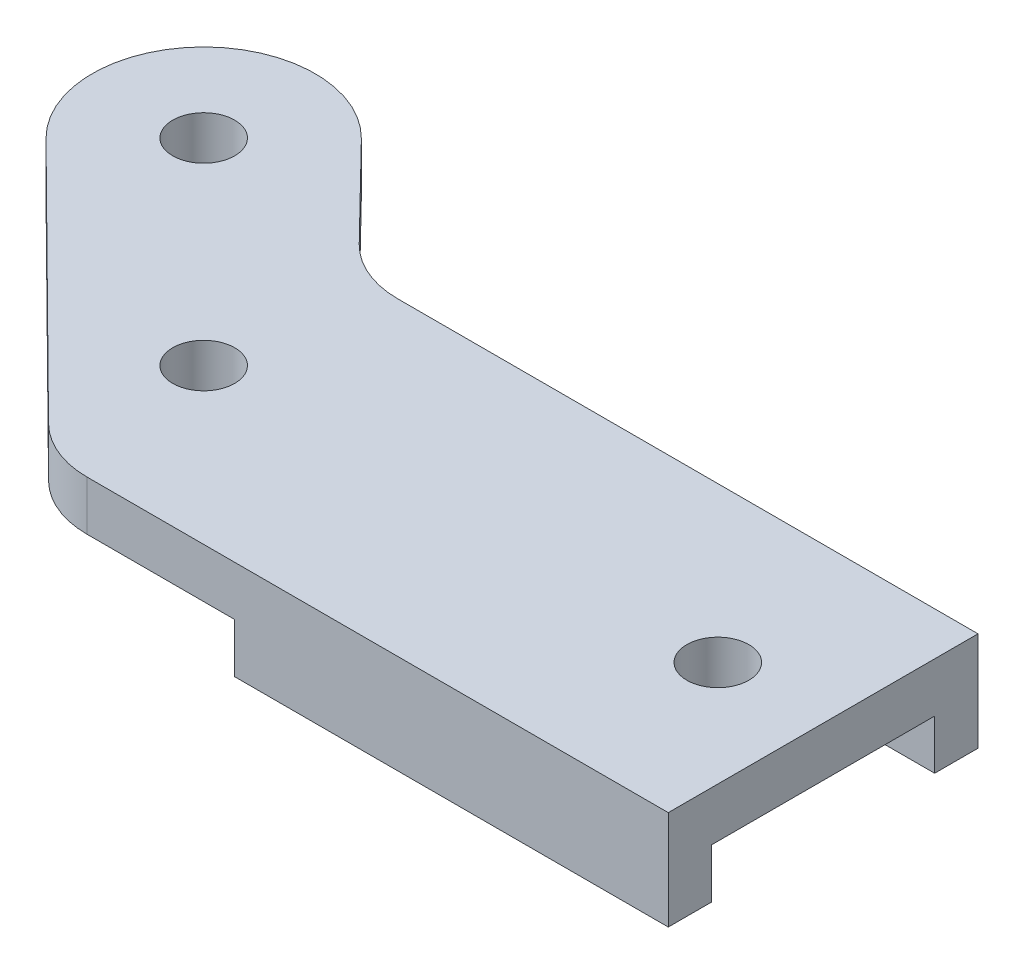
SolidWorks part; units mm, degrees
ref_plane "Front Plane" through (0, 0, 0) normal (0, 0, 1) x (1, 0, 0)
ref_plane "Top Plane" through (0, 0, 0) normal (0, 1, 0) x (1, 0, 0)
ref_plane "Right Plane" through (0, 0, 0) normal (1, 0, 0) x (0, 0, -1)
sketch "Sketch1" plane through (0, 0, 0) normal (0, 1, 0) x (1, 0, 0)
  line L0 (0, 0) -> (100, 0) construction
  line L1 (0, -25) -> (100, -25)
  line L2 (0, 25) -> (100, 25)
  line L3 (0, 0) -> (-31.8198, 31.8198) construction
  line L4 (0, 25) -> (-18.942, 44.3961)
  line L5 (0, -25) -> (-44.4821, 19.0265)
  line L6 (100, 25) -> (100, -25)
  circle A0 centre (-31.8198, 31.8198) radius 5
  circle A1 centre (0, 0) radius 5
  circle A2 centre (83, 0) radius 5
  arc A3 (-18.942, 44.3961) -> (-44.4821, 19.0265) centre (-31.8198, 31.8198) ccw
  dimension "D5" = 36
  dimension "D1" = 100
  dimension "D3" = 45
  dimension "D4" = 135
  dimension "D6" = 17
  dimension "D2" = 25
extrude "Boss-Extrude1" add sketch "Sketch1" along normal blind 8
sketch "Sketch2" plane through (0, 0, 0) normal (0, -1, 0) x (1, 0, 0)
  line L0 (100, 25) -> (30, 25)
  line L1 (0, 25) -> (100, 25) construction
  line L2 (30, 25) -> (30, -25)
  line L3 (100, -25) -> (0, -25) construction
  line L4 (30, -25) -> (100, -25)
  line L5 (100, -25) -> (100, -18)
  line L6 (100, 25) -> (100, -25) construction
  line L7 (100, -18) -> (50, -18)
  line L8 (50, -18) -> (50, 18)
  line L9 (50, 18) -> (100, 18)
  line L10 (100, 18) -> (100, 25)
  point P16 (100, -21.5)
  dimension "D1" = 36
  dimension "D2" = 70
  dimension "D3" = 50
extrude "Boss-Extrude2" add sketch "Sketch2" along normal blind 8
fillet "Fillet1" radius 15 2 edges at (0, 4, 25) (0, 4, -25)
